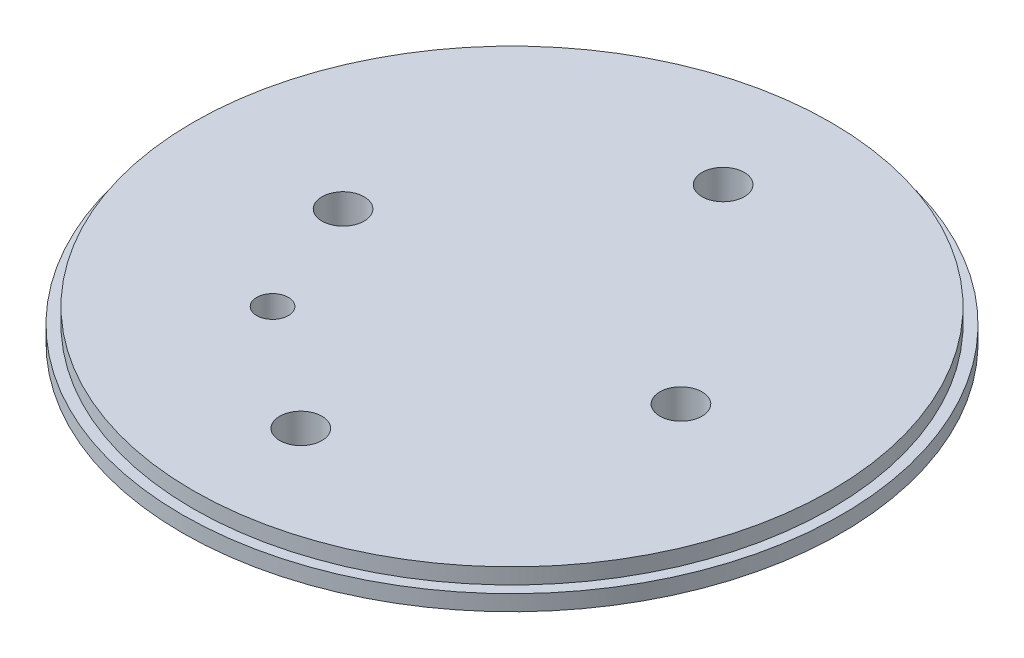
SolidWorks part; units mm, degrees
ref_plane "Front Plane" through (0, 0, 0) normal (0, 0, 1) x (1, 0, 0)
ref_plane "Top Plane" through (0, 0, 0) normal (0, 1, 0) x (1, 0, 0)
ref_plane "Right Plane" through (0, 0, 0) normal (1, 0, 0) x (0, 0, -1)
sketch "Sketch1" plane through (0, 0, 0) normal (0, 1, 0) x (1, 0, 0)
  circle A0 centre (0, 0) radius 49.55
  dimension "D1" = 99.1
extrude "Boss-Extrude1" add sketch "Sketch1" along normal blind 2.36
sketch "Sketch2" plane through (0, 2.36, 0) normal (0, 1, 0) x (1, 0, 0)
  circle A0 centre (0, 0) radius 47.95
  dimension "D1" = 95.9
extrude "Boss-Extrude2" add sketch "Sketch2" along normal blind 2.36 contours A0
sketch "Sketch3" plane through (0, 0, 0) normal (0, -1, 0) x (1, 0, 0)
  circle A0 centre (25.4, 0) radius 3.175
  circle A1 centre (-25.4, 0) radius 3.175
  circle A2 centre (0, 31.75) radius 3.175
  circle A3 centre (0, -31.75) radius 3.175
  circle A4 centre (-18, 18) radius 2.38
  dimension "D1" = 6.35
  dimension "D2" = 6.35
  dimension "D3" = 6.35
  dimension "D4" = 6.35
  dimension "D5" = 50.8
  dimension "D7" = 31.75
  dimension "D8" = 31.75
  dimension "D9" = 4.76
  dimension "D10" = 18
  dimension "D11" = 18
  dimension "D6" = 25.4
extrude "Cut-Extrude1" cut sketch "Sketch3" against normal through all
